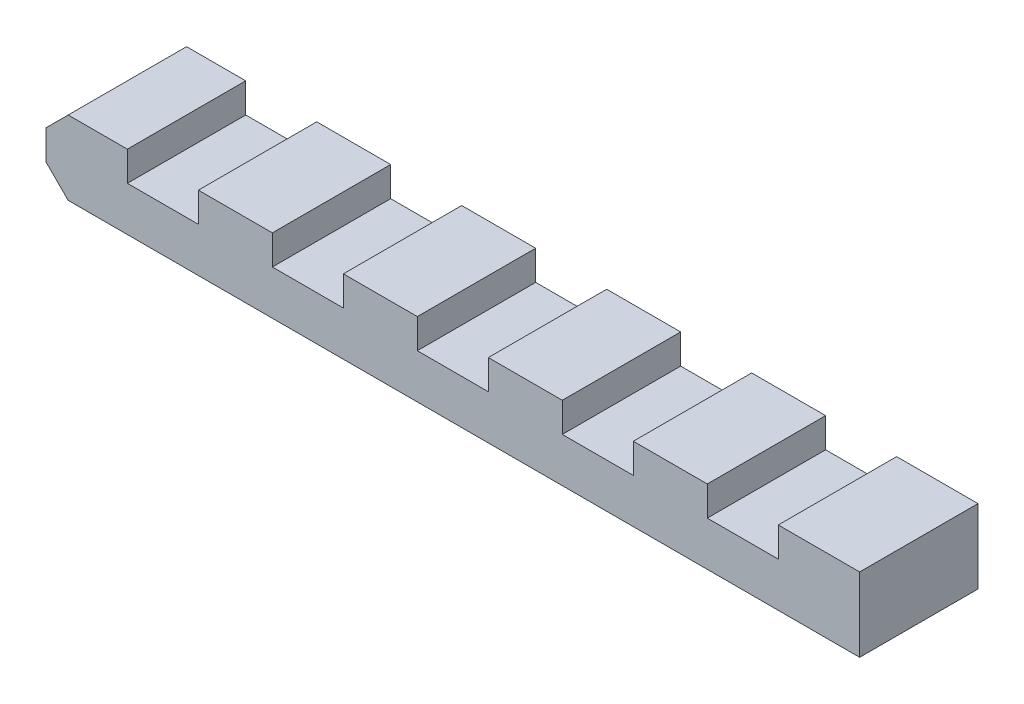
SolidWorks part; units mm, degrees
ref_plane "前视基准面" through (0, 0, 0) normal (0, 0, 1) x (1, 0, 0)
ref_plane "上视基准面" through (0, 0, 0) normal (0, 1, 0) x (1, 0, 0)
ref_plane "右视基准面" through (0, 0, 0) normal (1, 0, 0) x (0, 0, -1)
other "Configuration Table"
sketch "草图1" plane through (0, 0, 0) normal (0, 1, 0) x (1, 0, 0)
  line L1 (-27.5, -4) -> (27.5, -4)
  line L2 (-27.5, -4) -> (-27.5, 4)
  line L3 (-27.5, 4) -> (27.5, 4)
  line L4 (27.5, -4) -> (27.5, 4)
  line L5 (-27.5, -4) -> (27.5, 4) construction
  line L6 (-27.5, 4) -> (27.5, -4) construction
  point P0 (0, 0)
  dimension "D1" = 55
  dimension "D2" = 8
extrude "凸台-拉伸1" add sketch "草图1" along normal blind 5
sketch "草图2" plane through (0, 0, 4) normal (0, 0, 1) x (1, 0, 0)
  line L0 (-27.5, 5) -> (27.5, 5) construction
  line L1 (-22, 5) -> (-17.2, 5)
  line L2 (-22, 5) -> (-22, 3)
  line L3 (-22, 3) -> (-17.2, 3)
  line L4 (-17.2, 5) -> (-17.2, 3)
  line L5 (-12.2, 5) -> (-12.2, 3)
  line L6 (-12.2, 5) -> (-7.4, 5)
  line L7 (-7.4, 5) -> (-7.4, 3)
  line L8 (-12.2, 3) -> (-7.4, 3)
  line L9 (-2.4, 5) -> (-2.4, 3)
  line L10 (-2.4, 5) -> (2.4, 5)
  line L11 (2.4, 5) -> (2.4, 3)
  line L12 (-2.4, 3) -> (2.4, 3)
  line L13 (7.4, 5) -> (7.4, 3)
  line L14 (7.4, 5) -> (12.2, 5)
  line L15 (12.2, 5) -> (12.2, 3)
  line L16 (7.4, 3) -> (12.2, 3)
  line L17 (17.2, 5) -> (17.2, 3)
  line L18 (17.2, 5) -> (22, 5)
  line L19 (22, 5) -> (22, 3)
  line L20 (17.2, 3) -> (22, 3)
  line L23 (0, 0) -> (0, 12.4863) construction
  point P6 (0, 0)
  point P24 (12.3033, 5)
  dimension "D2" = 2
  dimension "D3" = 4.8
  dimension "D4" = 4.8
  dimension "D5" = 5
  dimension "D1" = 5
extrude "切除-拉伸1" cut sketch "草图2" against normal through all
chamfer "倒角1" distance 1.5 angle 45 2 edges at (-27.5, 0, 0) (-27.5, 5, 0)
